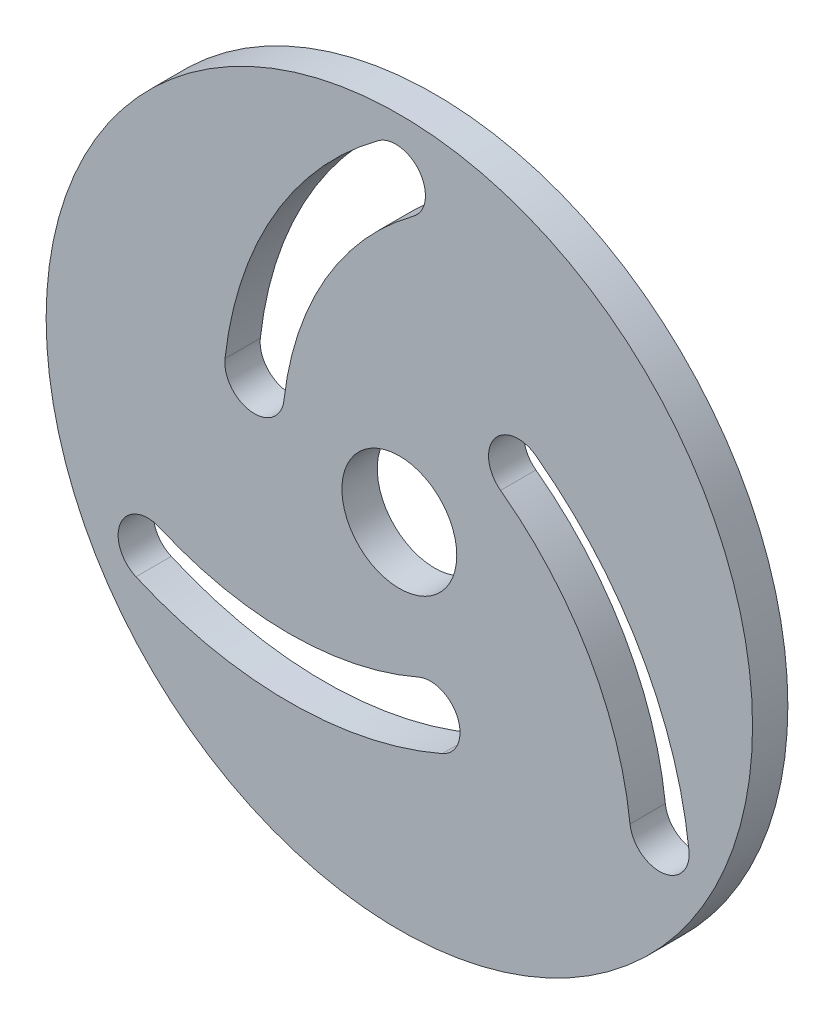
SolidWorks part; units mm, degrees
ref_plane "Front" through (0, 0, 0) normal (0, 0, 1) x (1, 0, 0)
ref_plane "Top" through (0, 0, 0) normal (0, 1, 0) x (1, 0, 0)
ref_plane "Right" through (0, 0, 0) normal (1, 0, 0) x (0, 0, -1)
sketch "Sketch1" plane through (0, 0, 0) normal (0, 0, 1) x (1, 0, 0)
  line L1 (-28.6551, 19.9015) -> (-16.5942, 40.7916) construction
  line L2 (-21.5946, 6.5744) -> (15.0791, 6.5744) construction
  line L3 (-21.5946, 6.5744) -> (-21.5946, 42.6831) construction
  circle A1 centre (-21.5946, 6.5744) radius 4.064
  circle A2 centre (-21.5946, 6.5744) radius 25
  circle A15 centre (-21.5946, 6.5744) radius 2.5625 construction
  circle A33 centre (-31.8476, 10.1977) radius 2.1 construction
  circle A36 centre (-13.1811, 13.7966) radius 2.1 construction
  arc A37 (-31.8476, 10.1977) -> (-21.8476, 27.5182) centre (-7.0045, 7.4015) cw construction
  circle A39 centre (-19.3977, -4.1685) radius 2.1 construction
  arc A40 (-23.0945, 29.208) -> (-33.9345, 10.4326) centre (-7.0045, 7.4015) ccw
  arc A41 (-20.6008, 25.8284) -> (-29.7608, 9.9628) centre (-7.0045, 7.4015) ccw
  arc A42 (-20.6008, 25.8284) -> (-23.0945, 29.208) centre (-21.8476, 27.5182) ccw
  arc A43 (-33.9345, 10.4326) -> (-29.7608, 9.9628) centre (-31.8476, 10.1977) ccw
  arc A44 (-5.268, -3.7588) -> (-14.428, 12.1068) centre (-28.0243, -6.3201) ccw
  arc A45 (-5.268, -3.7588) -> (-1.0943, -3.289) centre (-3.1811, -3.5239) ccw
  arc A46 (-11.9343, 15.4864) -> (-14.428, 12.1068) centre (-13.1811, 13.7966) ccw
  arc A47 (-1.0943, -3.289) -> (-11.9343, 15.4864) centre (-28.0243, -6.3201) ccw
  arc A48 (-13.1811, 13.7966) -> (-3.1811, -3.5239) centre (-28.0243, -6.3201) cw construction
  arc A49 (-38.5577, -2.2438) -> (-20.2377, -2.2438) centre (-29.3977, 18.7444) ccw
  arc A50 (-38.5577, -2.2438) -> (-40.2377, -6.0932) centre (-39.3977, -4.1685) ccw
  arc A51 (-18.5577, -6.0932) -> (-20.2377, -2.2438) centre (-19.3977, -4.1685) ccw
  arc A52 (-40.2377, -6.0932) -> (-18.5577, -6.0932) centre (-29.3977, 18.7444) ccw
  arc A53 (-19.3977, -4.1685) -> (-39.3977, -4.1685) centre (-29.3977, 18.7444) cw construction
  point P8 (-28.6551, 19.9015)
  point P32 (-6.3736, 6.1799)
  point P40 (-29.3977, -6.2556)
  dimension "D1" = 50
  dimension "D2" = 4.2
  dimension "D5" = 25
  dimension "D7" = 8.128
  dimension "D6" = 20
  dimension "115" = 60
  dimension "D3" = 3.6233
  dimension "D4" = 10.253
  dimension "D9" = 8.4134
  dimension "D10" = 7.2222
  dimension "D8" = 3
extrude "Boss-Extrude1" add sketch "Sketch1" along normal blind 2.5 contours A47 A45 A2 A44 A46 A52 A50 A49 A51 A43 A40 A42 A41 A1
